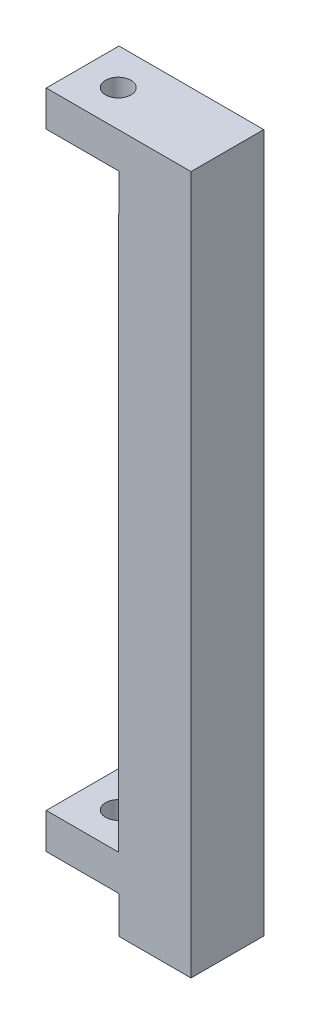
SolidWorks part; units mm, degrees
ref_plane "Front Plane" through (0, 0, 0) normal (0, 0, 1) x (1, 0, 0)
ref_plane "Top Plane" through (0, 0, 0) normal (0, 1, 0) x (1, 0, 0)
ref_plane "Right Plane" through (0, 0, 0) normal (1, 0, 0) x (0, 0, -1)
sketch "Sketch1" plane through (0, 0, 0) normal (0, 0, 1) x (1, 0, 0)
  line L0 (0, 0) -> (0, 5)
  line L1 (0, 5) -> (-10, 5)
  line L2 (-10, 5) -> (-10, 10)
  line L3 (-10, 10) -> (0, 10)
  line L4 (0, 10) -> (0, 91)
  line L5 (0, 91) -> (-10, 91)
  line L6 (-10, 91) -> (-10, 96)
  line L7 (-10, 96) -> (10, 96)
  line L10 (10, 96) -> (10, 0)
  line L11 (10, 0) -> (0, 0)
  dimension "D1" = 10
  dimension "D2" = 5
  dimension "D3" = 5
  dimension "D4" = 5
  dimension "D6" = 10
  dimension "D7" = 10
  dimension "D8" = 81
extrude "Boss-Extrude1" add sketch "Sketch1" against normal blind 10
sketch "Sketch2" plane through (0, 0, 0) normal (0, 0, 1) x (1, 0, 0)
  line L0 (-10, 10) -> (-10, 5)
  line L1 (-10, 5) -> (0, 5)
  line L2 (0, 5) -> (0, 0)
  line L3 (-10, 96) -> (-10, 91)
  line L4 (-10, 91) -> (0, 91)
  line L5 (0, 91) -> (0, 85.9)
  line L6 (0, 91) -> (0, 10) construction
  line L7 (-9.9, 96) -> (-9.9, 91.1)
  line L8 (-9.9, 91.1) -> (0.1, 91.1)
  line L9 (0.1, 91.1) -> (0.1, 85.9)
  line L10 (-9.9, 10) -> (-9.9, 5.1)
  line L11 (-9.9, 5.1) -> (0.1, 5.1)
  line L12 (0.1, 5.1) -> (0.1, 0)
  line L13 (-10, 10) -> (-9.9, 10)
  line L14 (0, 0) -> (0.1, 0)
  line L15 (0, 85.9) -> (0.1, 85.9)
  line L16 (-10, 96) -> (-9.9, 96)
  dimension "D1" = 5.1
  dimension "D2" = 0.1
extrude "Cut-Extrude1" cut sketch "Sketch2" against normal through all
sketch "Sketch3" plane through (0, 5.1, 0) normal (0, -1, 0) x (1, 0, 0)
  line L0 (0.1, -10) -> (-9.9, -10) construction
  line L1 (-10, 0) -> (0, 0) construction
  line L2 (-10, 0) -> (-10, -10) construction
  line L3 (-10, -10) -> (0, -10) construction
  line L4 (0, 0) -> (0, -10) construction
  line L5 (-9.9, -10) -> (-9.9, 0) construction
  line L6 (0.1, -10) -> (0.1, 0) construction
  line L7 (0.1, 0) -> (-9.9, 0) construction
  line L8 (-10, 0) -> (0, -10) construction
  circle A0 centre (-5, -5) radius 1.75
  dimension "D3" = 3.5
  dimension "D1" = 0.1
  dimension "D2" = 0.1
extrude "Cut-Extrude2" cut sketch "Sketch3" against normal through all
